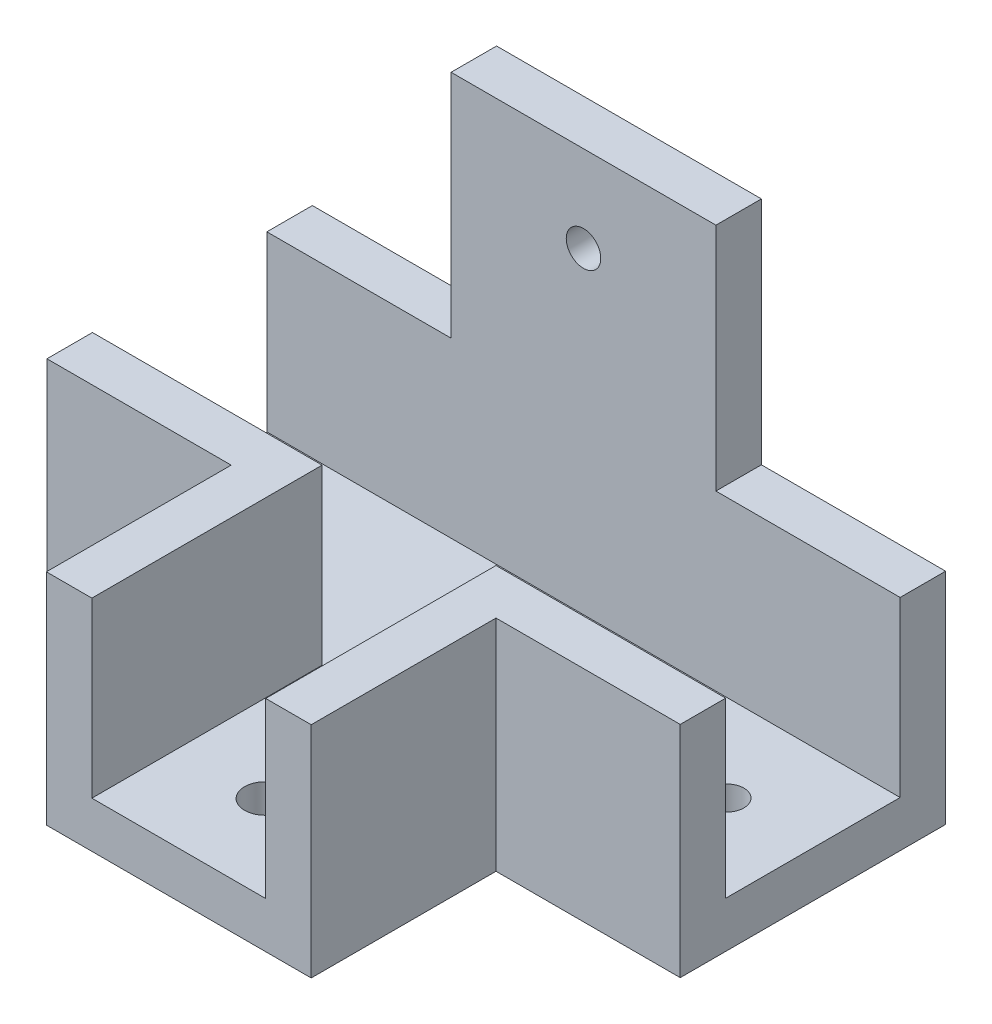
SolidWorks part; units mm, degrees
ref_plane "前视基准面" through (0, 0, 0) normal (0, 0, 1) x (1, 0, 0)
ref_plane "上视基准面" through (0, 0, 0) normal (0, 1, 0) x (1, 0, 0)
ref_plane "右视基准面" through (0, 0, 0) normal (1, 0, 0) x (0, 0, -1)
sketch "草图1" plane through (0, 0, 0) normal (0, 1, 0) x (1, 0, 0)
  line L1 (-40.9114, -1.4852) -> (14.0886, -1.4852)
  line L2 (-40.9114, -1.4852) -> (-40.9114, 17.6148)
  line L3 (-40.9114, 17.6148) -> (14.0886, 17.6148)
  line L4 (14.0886, -1.4852) -> (14.0886, 17.6148)
  dimension "D1" = 55
  dimension "D2" = 19.1
extrude "凸台-拉伸1" add sketch "草图1" along normal blind 4
sketch "草图2" plane through (0, 4, 0) normal (0, 1, 0) x (1, 0, 0)
  line L0 (14.0886, -1.4852) -> (14.0886, 17.6148) construction
  line L1 (-40.9114, 17.6148) -> (14.0886, 17.6148)
  line L2 (-40.9114, 17.6148) -> (-40.9114, 13.6648)
  line L3 (-40.9114, 13.6648) -> (14.0886, 13.6648)
  line L4 (14.0886, 17.6148) -> (14.0886, 13.6648)
  dimension "D1" = 3.95
extrude "凸台-拉伸2" add sketch "草图2" along normal blind 15.05
sketch "草图3" plane through (0, 0, 0) normal (0, -1, 0) x (1, 0, 0)
  line L0 (14.0886, 1.4852) -> (14.0886, -17.6148) construction
  line L1 (-40.9114, 1.4852) -> (14.0886, 1.4852)
  line L2 (-40.9114, 1.4852) -> (-40.9114, 5.4352)
  line L3 (-40.9114, 5.4352) -> (-24.9114, 5.4352)
  line L4 (14.0886, 1.4852) -> (14.0886, 5.4352)
  line L5 (-1.9114, 5.4352) -> (14.0886, 5.4352)
  line L6 (-28.9114, 1.4852) -> (-5.9114, 1.4852)
  line L7 (-24.9114, 5.4352) -> (-24.9114, 21.4852)
  line L8 (-24.9114, 21.4852) -> (-1.9114, 21.4852)
  line L9 (-1.9114, 5.4352) -> (-1.9114, 21.4852)
  point P13 (0, 0)
  point P14 (0, 0)
  line M12 (14.0886, 1.4852) -> (-40.9114, 1.4852)
  dimension "D1" = 3.95
  dimension "D2" = 20
  dimension "D3" = 16
  dimension "D4" = 23
extrude "凸台-拉伸3" add sketch "草图3" against normal blind 4 separate body contours L5 L9 L8 L7 L3 L2 L1 L4 M12
sketch "草图4" plane through (0, 4, 0) normal (0, 1, 0) x (1, 0, 0)
  line L0 (14.0886, -1.4852) -> (-40.9114, -1.4852) construction
  line L1 (14.0886, -5.4352) -> (-5.8614, -5.4352)
  line L2 (14.0886, -5.4352) -> (14.0886, -1.4852)
  line L3 (14.0886, -1.4852) -> (-5.8614, -1.4852)
  line L4 (-5.8614, -5.4352) -> (-5.8614, -1.4852)
  line L6 (-5.8614, -5.4352) -> (-1.9114, -5.4352)
  line L7 (-5.8614, -5.4352) -> (-5.8614, -21.4852)
  line L8 (-5.8614, -21.4852) -> (-1.9114, -21.4852)
  line L9 (-1.9114, -5.4352) -> (-1.9114, -21.4852)
  line L10 (-24.9114, -21.4852) -> (-20.9614, -21.4852)
  line L11 (-24.9114, -21.4852) -> (-24.9114, -1.4852)
  line L12 (-24.9114, -1.4852) -> (-20.9614, -1.4852)
  line L13 (-20.9614, -21.4852) -> (-20.9614, -1.4852)
  line L14 (-24.9114, -5.4352) -> (-40.9114, -5.4352)
  line L15 (-24.9114, -5.4352) -> (-24.9114, -1.4852)
  line L16 (-24.9114, -1.4852) -> (-40.9114, -1.4852)
  line L17 (-40.9114, -5.4352) -> (-40.9114, -1.4852)
  line M6 (-1.9114, -5.4352) -> (14.0886, -5.4352)
  line M7 (14.0886, -5.4352) -> (14.0886, -1.4852)
  line M8 (14.0886, -1.4852) -> (-40.9114, -1.4852)
  line M9 (-40.9114, -1.4852) -> (-40.9114, -5.4352)
  line M10 (-40.9114, -5.4352) -> (-24.9114, -5.4352)
  line M11 (-24.9114, -5.4352) -> (-24.9114, -21.4852)
  line M12 (-24.9114, -21.4852) -> (-1.9114, -21.4852)
  line M13 (-1.9114, -21.4852) -> (-1.9114, -5.4352)
  dimension "D1" = 3.95
  dimension "D2" = 3.95
extrude "凸台-拉伸4" add sketch "草图4" along normal blind 15.05 contours L1 L7 M12 M13 | L4 L1 M6 M7 M8 | L13 L11 M12 M8 M11 | L11 M10 M8 M9
sketch "草图5" plane through (0, 0, -17.6148) normal (0, 0, -1) x (-1, 0, 0)
  line L0 (-14.0886, 19.05) -> (40.9114, 19.05) construction
  line L1 (1.9114, 19.05) -> (24.9114, 19.05)
  line L2 (1.9114, 19.05) -> (1.9114, 39.05)
  line L3 (1.9114, 39.05) -> (24.9114, 39.05)
  line L4 (24.9114, 19.05) -> (24.9114, 39.05)
  line L5 (-14.0886, 19.05) -> (-14.0886, 0) construction
  dimension "D1" = 16
  dimension "D2" = 23
  dimension "D3" = 20
extrude "凸台-拉伸5" add sketch "草图5" against normal blind 3.95
sketch "草图6" plane through (0, 0, -17.6148) normal (0, 0, -1) x (-1, 0, 0)
  line L0 (24.9114, 39.05) -> (1.9114, 39.05) construction
  circle A0 centre (13.4114, 31.55) radius 1.5
  dimension "D1" = 3
  dimension "D2" = 7.5
extrude "切除-拉伸1" cut sketch "草图6" against normal blind 4
sketch "草图7" plane through (0, 0, 0) normal (0, -1, 0) x (1, 0, 0)
  line L0 (14.0886, 5.4352) -> (14.0886, -17.6148) construction
  line L1 (-40.9114, -17.6148) -> (-40.9114, 5.4352) construction
  line L2 (-24.9114, 21.4852) -> (-1.9114, 21.4852) construction
  circle A0 centre (6.5886, -6.0898) radius 1.5
  circle A1 centre (-33.4114, -6.0898) radius 1.5
  circle A2 centre (-13.4114, 13.9852) radius 1.7851
  dimension "D1" = 3
  dimension "D2" = 3
  dimension "D3" = 7.5
  dimension "D4" = 7.5
  dimension "D5" = 7.5
extrude "切除-拉伸2" cut sketch "草图7" against normal blind 4
